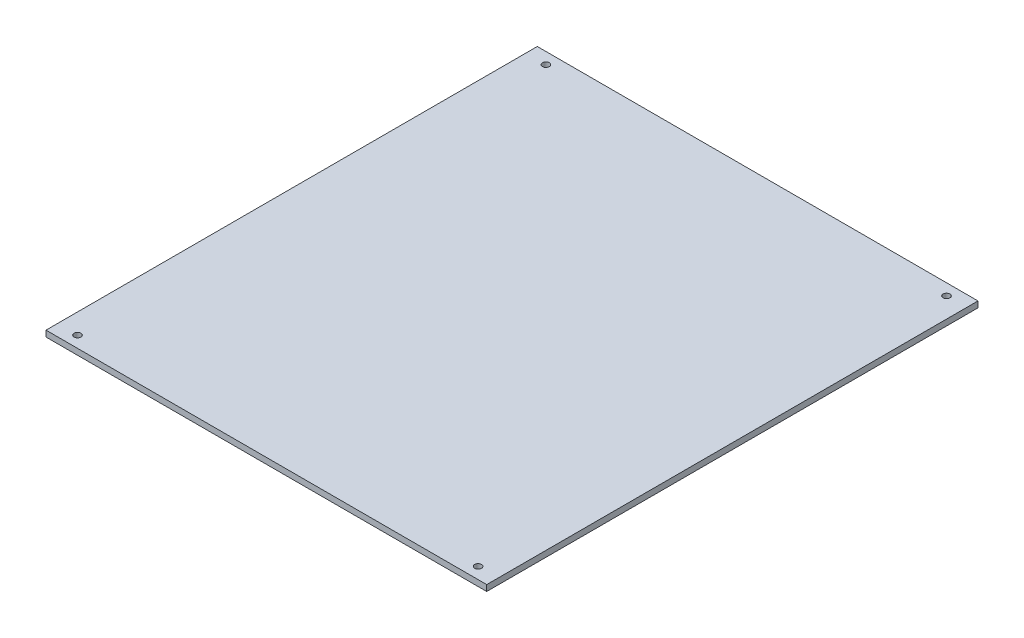
SolidWorks part; units mm, degrees
ref_plane "Plan de face" through (0, 0, 0) normal (0, 0, 1) x (1, 0, 0)
ref_plane "Plan de dessus" through (0, 0, 0) normal (0, 1, 0) x (1, 0, 0)
ref_plane "Plan de droite" through (0, 0, 0) normal (1, 0, 0) x (0, 0, -1)
sketch "Esquisse1" plane through (0, 0, 0) normal (0, 0, 1) x (1, 0, 0)
  line L0 (-40.2843, 0) -> (179.4857, 0)
  dimension "D1" = 219.77
extrude "Extru.-Mince1" add sketch "Esquisse1" along normal blind 245 thin
sketch "Esquisse2" plane through (0, 0, 0) normal (0, 1, 0) x (1, 0, 0)
  line L0 (-40.2843, 0) -> (179.4857, 0) construction
  line L2 (-40.2843, -245) -> (179.4857, -245) construction
  line L3 (-40.2843, -245) -> (-40.2843, 0) construction
  line L4 (179.4857, -245) -> (179.4857, 0) construction
  point P0 (-30.2843, -5.7)
  point P1 (169.4857, -5.7)
  point P2 (169.4857, -239.3)
  point P3 (-30.2843, -239.3)
  dimension "D1" = 5.7
  dimension "D2" = 5.7
  dimension "D3" = 5.7
  dimension "D4" = 5.7
  dimension "D5" = 10
  dimension "D6" = 10
  dimension "D7" = 10
  dimension "D8" = 10
hole_wizard "Dégagement M31" positions "Esquisse4" profile "Esquisse3" hole size "M3" standard "ISO" end condition through all
sketch "Esquisse4" plane through (0, 0, 0) normal (0, 1, 0) x (-1, 0, 0)
  point P1 (30.2843, 5.7)
  point P4 (-169.4857, 5.7)
  point P7 (30.2843, 239.3)
  point P10 (-169.4857, 239.3)
sketch "Esquisse3" plane through (-30.2843, 0, 5.7) normal (1, 0, 0) x (0, 0, 1)
  line L0 (0, 0) -> (0, 3)
  line L1 (0, 3) -> (1.7, 3)
  line L2 (1.7, 3) -> (1.7, 0)
  line L5 (1.7, 0) -> (0, 0)
  line L11 (0, -6.35) -> (0, 107.95) construction
  dimension "Diamètre du perçage jusqu'au prochain" = 3.4
  dimension "Profondeur du perçage jusqu'au prochain" = 3
